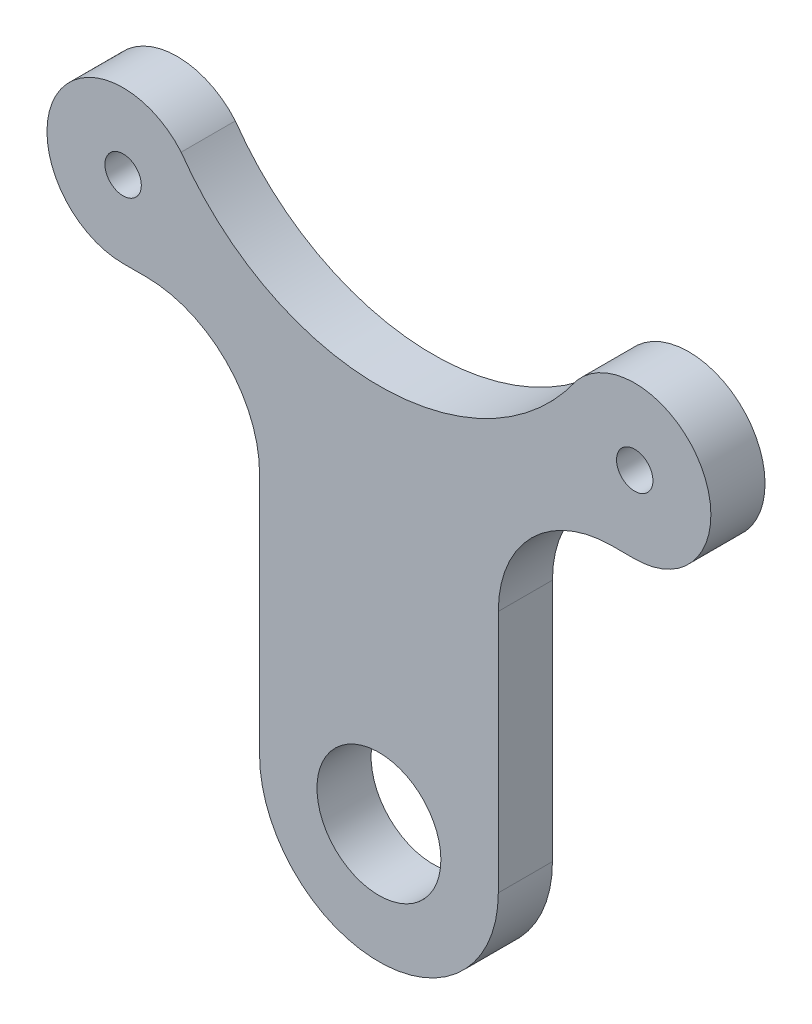
SolidWorks part; units mm, degrees
material "6061-T6 (SS)"
ref_plane "Front Plane" through (0, 0, 0) normal (0, 0, 1) x (1, 0, 0)
ref_plane "Top Plane" through (0, 0, 0) normal (0, 1, 0) x (1, 0, 0)
ref_plane "Right Plane" through (0, 0, 0) normal (1, 0, 0) x (0, 0, -1)
sketch "Sketch1" plane through (0, 0, 0) normal (0, 0, 1) x (1, 0, 0)
  line L0 (0, 33.3742) -> (0, 5.4494) construction
  line L1 (-22.5, 38.1393) -> (22.5, 38.1393) construction
  line L2 (20.5, 31.4393) -> (22.5, 31.4393)
  line L3 (0, 33.3742) -> (0, 38.1393) construction
  line L4 (-5, 38.1393) -> (-5, 5.4494) construction
  line L5 (-22.5, 31.4393) -> (-20.5, 31.4393)
  line L6 (0, 5.4494) -> (-13.0161, 5.4494) construction
  line L7 (5, 38.1393) -> (5, 5.4494) construction
  line L8 (-10.5, 21.4393) -> (-10.5, 0)
  line L9 (0, 5.4494) -> (18.2252, 5.4494) construction
  line L10 (10.5, 21.4393) -> (10.5, 0)
  circle A0 centre (-22.5, 38.1393) radius 1.7 construction
  circle A1 centre (22.5, 38.1393) radius 1.7 construction
  circle A2 centre (0, 0) radius 5.4494
  arc A3 (-10.5, 0) -> (10.5, 0) centre (0, 0) ccw
  arc A5 (-16.8073, 41.6724) -> (-22.5, 31.4393) centre (-22.5, 38.1393) ccw
  arc A6 (-10.5, 21.4393) -> (-20.5, 31.4393) centre (-20.5, 21.4393) ccw
  arc A7 (10.5, 21.4393) -> (20.5, 31.4393) centre (20.5, 21.4393) cw
  arc A8 (-17.3952, 42.4788) -> (17.3952, 42.4788) centre (0, 54.544) ccw
  arc A10 (22.5, 31.4393) -> (16.8073, 41.6724) centre (22.5, 38.1393) ccw
  point P9 (5, 38.1393)
  point P21 (-5, 38.1393)
  point P25 (0, 19.4118)
  point P28 (-5, 16.0159)
  point P29 (5, 15.9441)
  point P30 (0, -10.5)
  point P35 (22.5, 44.8393)
  point P37 (0, 44.8393)
  point P38 (-29.2, 38.1393)
  point P39 (29.2, 38.1393)
  dimension "D1" = 10
  dimension "D2" = 10
  dimension "D3" = 38.1393
  dimension "D4" = 58.4
  dimension "D5" = 55.3393
extrude "Boss-Extrude1" add sketch "Sketch1" along normal blind 4.763 contours L2 A10 A8 A5 L5 A6 L8 A3 L10 A7 A2
hole_wizard "M3 Clearance Hole1" positions "Sketch3" profile "Sketch2" hole size "M3" standard "ANSI Metric" end condition through all
sketch "Sketch3" plane through (0, 0, 4.763) normal (0, 0, 1) x (1, 0, 0)
  line L2 (0, 0) -> (0, 54.7774) construction
  point P0 (-22.5, 38.1959)
  point P2 (22.5, 38.1959)
  dimension "D1" = 45
  dimension "D2" = 22.5
  dimension "D3" = 22.5
sketch "Sketch2" plane through (-22.5, 38.1959, 4.763) normal (1, 0, 0) x (0, -1, 0)
  line L0 (0, 0) -> (0, 4.763)
  line L1 (0, 4.763) -> (1.6, 4.763)
  line L2 (1.6, 4.763) -> (1.6, 0)
  line L5 (1.6, 0) -> (0, 0)
  line L11 (0, -6.35) -> (0, 107.95) construction
  dimension "Thru Hole Dia." = 3.2
  dimension "Thru Hole Depth" = 4.763
